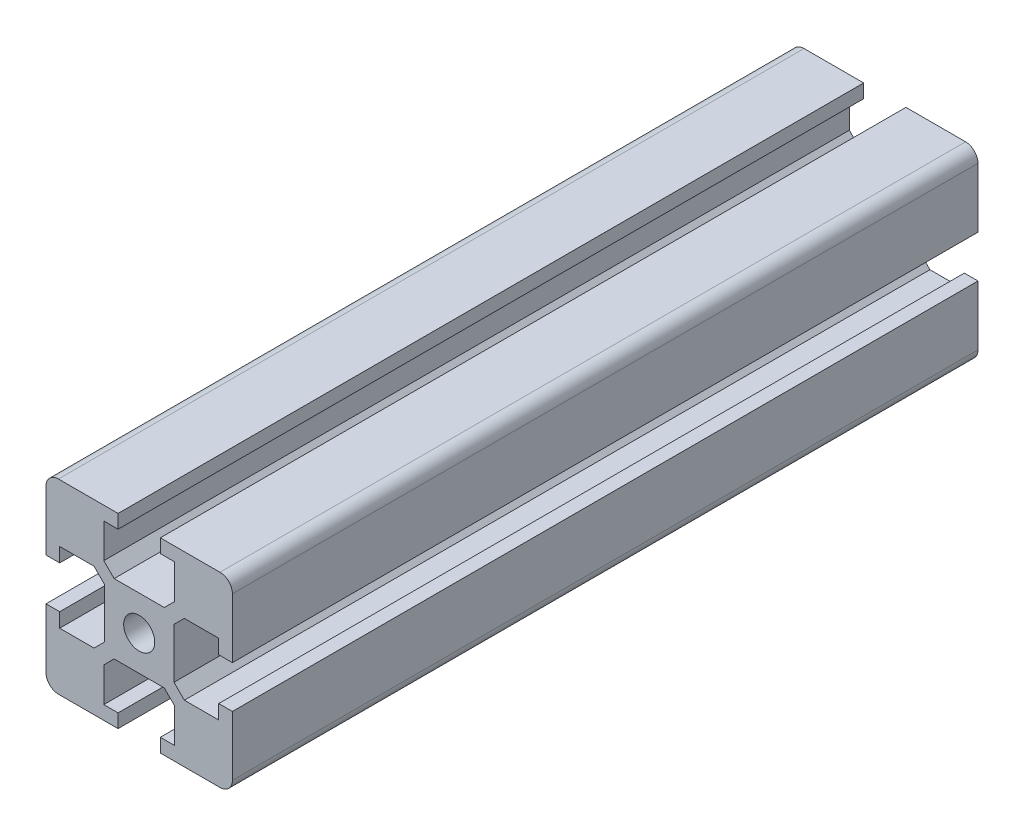
SolidWorks part; units mm, degrees
material "6061 Alloy"
ref_plane "Front Plane" through (0, 0, 0) normal (0, 0, 1) x (1, 0, 0)
ref_plane "Top Plane" through (0, 0, 0) normal (0, 1, 0) x (1, 0, 0)
ref_plane "Right Plane" through (0, 0, 0) normal (1, 0, 0) x (0, 0, -1)
sketch "Sketch1" plane through (0, 0, 0) normal (0, 0, 1) x (1, 0, 0)
  line L0 (0, 7.5) -> (0, -7.5) construction
  line L1 (7.5, 0) -> (-7.5, 0) construction
  line L2 (7.5, -7.5) -> (1.7, -7.5)
  line L3 (7.5, -7.5) -> (7.5, -1.7)
  line L4 (7.5, 7.5) -> (1.7, 7.5)
  line L5 (-7.5, -7.5) -> (-7.5, -1.7)
  line L6 (7.5, -7.5) -> (-7.5, 7.5) construction
  line L7 (7.5, 7.5) -> (-7.5, -7.5) construction
  line L8 (1.7, 7.5) -> (1.7, 6.4)
  line L9 (1.7, 6.4) -> (2.85, 6.4)
  line L10 (2.85, 6.4) -> (2.85, 3.6318)
  line L11 (2.85, 3.6318) -> (2.0182, 2.8)
  line L12 (2.0182, 2.8) -> (-2.0182, 2.8)
  line L13 (-2.85, 3.6318) -> (-2.0182, 2.8)
  line L14 (-2.85, 6.4) -> (-2.85, 3.6318)
  line L15 (-1.7, 6.4) -> (-2.85, 6.4)
  line L16 (-1.7, 7.5) -> (-1.7, 6.4)
  line L17 (6.4, -1.7) -> (6.4, -2.85)
  line L18 (7.5, -1.7) -> (6.4, -1.7)
  line L19 (6.4, -2.85) -> (3.6318, -2.85)
  line L20 (3.6318, -2.85) -> (2.8, -2.0182)
  line L21 (2.8, -2.0182) -> (2.8, 2.0182)
  line L22 (3.6318, 2.85) -> (2.8, 2.0182)
  line L23 (6.4, 2.85) -> (3.6318, 2.85)
  line L24 (6.4, 1.7) -> (6.4, 2.85)
  line L25 (7.5, 1.7) -> (6.4, 1.7)
  line L26 (-1.7, -6.4) -> (-2.85, -6.4)
  line L27 (-1.7, -7.5) -> (-1.7, -6.4)
  line L28 (-2.85, -6.4) -> (-2.85, -3.6318)
  line L29 (-2.85, -3.6318) -> (-2.0182, -2.8)
  line L30 (-2.0182, -2.8) -> (2.0182, -2.8)
  line L31 (2.85, -3.6318) -> (2.0182, -2.8)
  line L32 (2.85, -6.4) -> (2.85, -3.6318)
  line L33 (1.7, -6.4) -> (2.85, -6.4)
  line L34 (1.7, -7.5) -> (1.7, -6.4)
  line L35 (-6.4, 1.7) -> (-6.4, 2.85)
  line L36 (-7.5, 1.7) -> (-6.4, 1.7)
  line L37 (-6.4, 2.85) -> (-3.6318, 2.85)
  line L38 (-3.6318, 2.85) -> (-2.8, 2.0182)
  line L39 (-2.8, 2.0182) -> (-2.8, -2.0182)
  line L40 (-3.6318, -2.85) -> (-2.8, -2.0182)
  line L41 (-6.4, -2.85) -> (-3.6318, -2.85)
  line L42 (-6.4, -1.7) -> (-6.4, -2.85)
  line L43 (-7.5, -1.7) -> (-6.4, -1.7)
  line L44 (-1.7, 7.5) -> (-7.5, 7.5)
  line L45 (-7.5, 1.7) -> (-7.5, 7.5)
  line L46 (-1.7, -7.5) -> (-7.5, -7.5)
  line L47 (7.5, 1.7) -> (7.5, 7.5)
  circle A0 centre (0, 0) radius 1.25
  point P3 (0, 0)
  point P19 (0, 2.8)
  point P56 (0, 0)
  dimension "D3" = 2.5
  dimension "D2" = 15
  dimension "D4" = 1.1
  dimension "D5" = 3.6
  dimension "D6" = 5.7
  dimension "D7" = 3.4
  dimension "D8" = 4
extrude "Boss-Extrude1" add sketch "Sketch1" along normal blind 60
fillet "Fillet1" radius 1 4 edges at (7.5, -7.5, 30) (-7.5, -7.5, 30) (7.5, 7.5, 30) (-7.5, 7.5, 30)
equation "\"D1@Boss-Extrude1\"=60"
